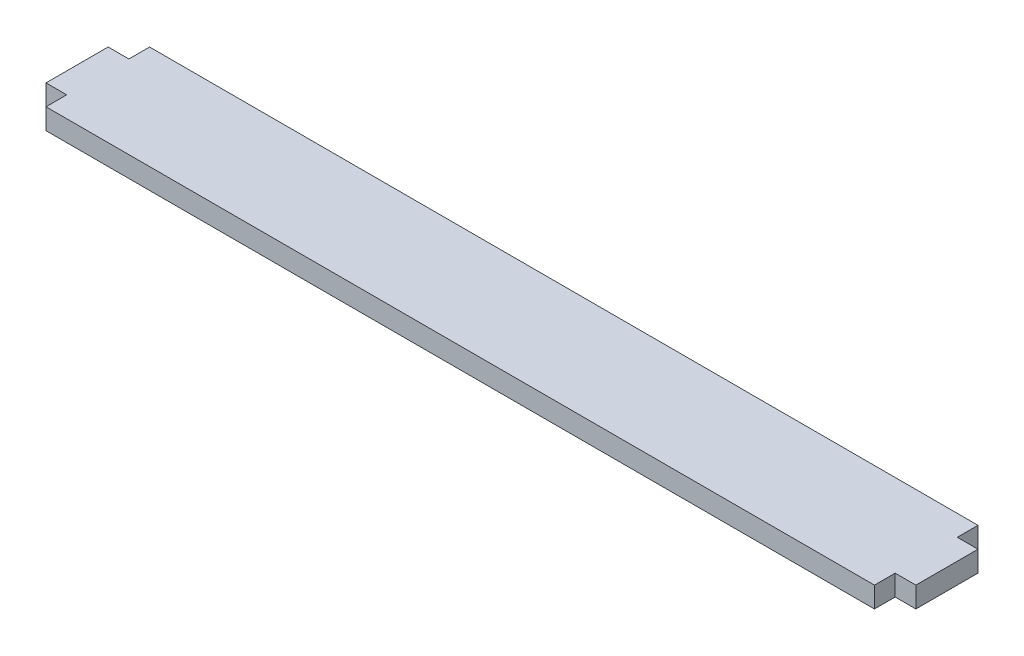
SolidWorks part; units mm, degrees
ref_plane "Front Plane" through (0, 0, 0) normal (0, 0, 1) x (1, 0, 0)
ref_plane "Top Plane" through (0, 0, 0) normal (0, 1, 0) x (1, 0, 0)
ref_plane "Right Plane" through (0, 0, 0) normal (1, 0, 0) x (0, 0, -1)
sketch "Sketch1" plane through (0, 0, 0) normal (0, 1, 0) x (1, 0, 0)
  line L0 (-63.5, -7.9375) -> (63.5, -7.9375)
  line L1 (63.5, -7.9375) -> (63.5, -4.7625)
  line L2 (63.5, -4.7625) -> (66.675, -4.7625)
  line L3 (66.675, -4.7625) -> (66.675, 4.7625)
  line L4 (66.675, 4.7625) -> (63.5, 4.7625)
  line L5 (63.5, 4.7625) -> (63.5, 7.9375)
  line L6 (63.5, 7.9375) -> (-63.5, 7.9375)
  line L7 (-63.5, 7.9375) -> (-63.5, 4.7625)
  line L8 (-63.5, 4.7625) -> (-66.675, 4.7625)
  line L9 (-66.675, 4.7625) -> (-66.675, -4.7625)
  line L10 (-66.675, -4.7625) -> (-63.5, -4.7625)
  line L11 (-63.5, -4.7625) -> (-63.5, -7.9375)
  point P9 (0, 7.9375)
  point P13 (66.675, 0)
  dimension "D1" = 3.175
  dimension "D2" = 9.525
  dimension "D3" = 15.875
  dimension "D4" = 127
extrude "Boss-Extrude1" add sketch "Sketch1" along normal blind 3.175
